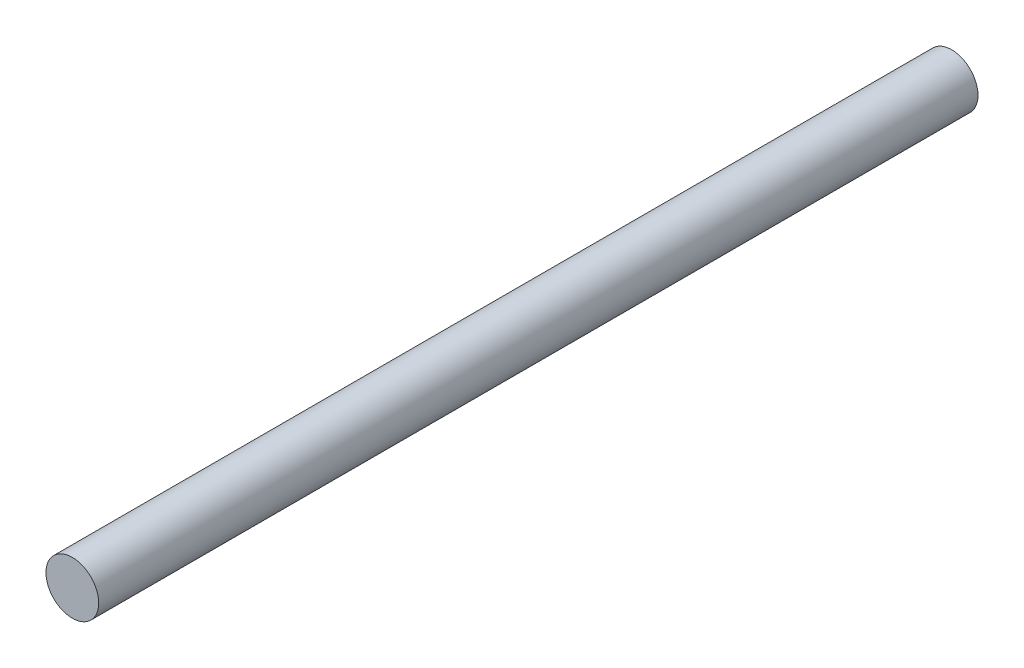
SolidWorks part; units mm, degrees
ref_plane "前视基准面" through (0, 0, 0) normal (0, 0, 1) x (1, 0, 0)
ref_plane "上视基准面" through (0, 0, 0) normal (0, 1, 0) x (1, 0, 0)
ref_plane "右视基准面" through (0, 0, 0) normal (1, 0, 0) x (0, 0, -1)
other "Configuration Table"
sketch "草图1" plane through (0, 0, 0) normal (0, 0, 1) x (1, 0, 0)
  circle A0 centre (-142.4403, 390.9122) radius 15
  dimension "D1" = 30
extrude "凸台-拉伸1" add sketch "草图1" along normal blind 500
